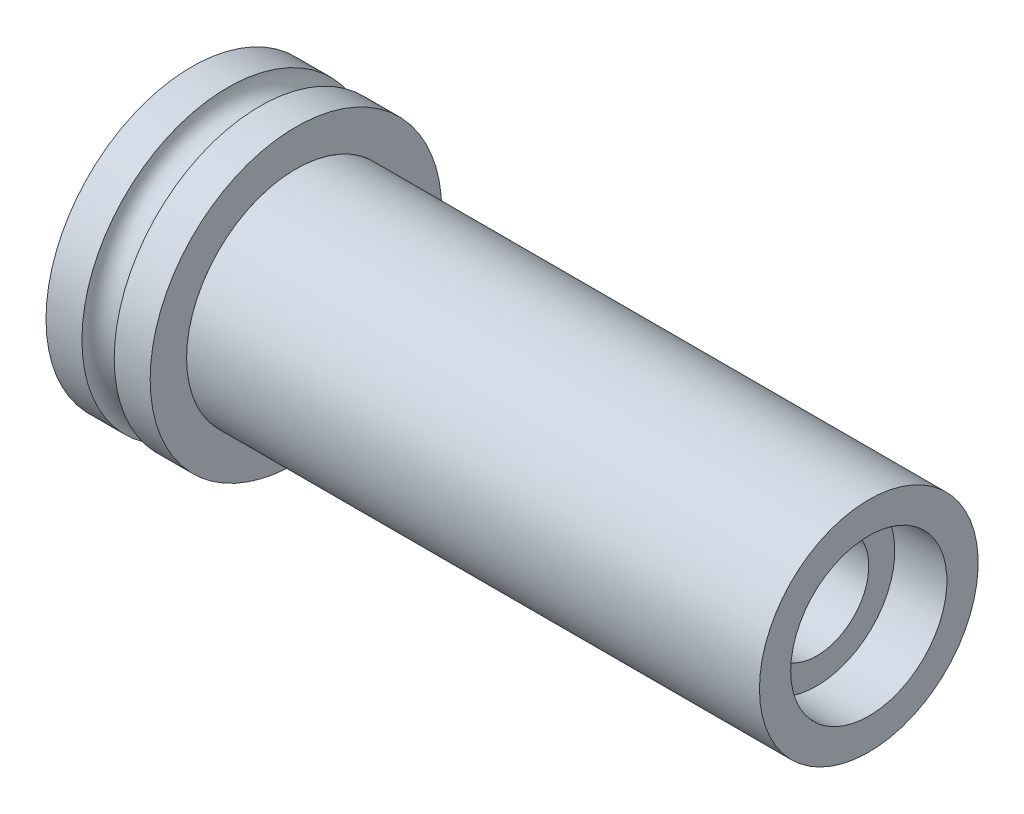
SolidWorks part; units mm, degrees
ref_plane "Front Plane" through (0, 0, 0) normal (0, 0, 1) x (1, 0, 0)
ref_plane "Top Plane" through (0, 0, 0) normal (0, 1, 0) x (1, 0, 0)
ref_plane "Right Plane" through (0, 0, 0) normal (1, 0, 0) x (0, 0, -1)
sketch "Sketch1" plane through (0, 0, 0) normal (0, 1, 0) x (1, 0, 0)
  line L0 (-27.5, 0) -> (27.5, 0) construction
  line L1 (-22.5, 7.5) -> (-22.5, 5)
  line L2 (-27.5, 10.5) -> (27.5, 10.5)
  line L3 (-27.5, 10.5) -> (-27.5, 7.5)
  line L4 (-27.5, 7.5) -> (-22.5, 7.5)
  line L5 (27.5, 10.5) -> (27.5, 7.5)
  line L6 (-27.5, 10.5) -> (27.5, 7.5) construction
  line L7 (-27.5, 7.5) -> (27.5, 10.5) construction
  line L8 (-22.5, 5) -> (22.5, 5)
  line L9 (22.5, 5) -> (22.5, 7.5)
  line L10 (22.5, 7.5) -> (27.5, 7.5)
  point P2 (0, 9)
  point P3 (0, 0)
  dimension "D1" = 55
  dimension "D2" = 3
  dimension "D3" = 7.5
  dimension "D4" = 5
  dimension "D5" = 5
  dimension "D6" = 5
revolve "Revolve1" add sketch "Sketch1" angle 360 about L0
sketch "Sketch2" plane through (-27.5, 0, 0) normal (1, 0, 0) x (0, 0, -1)
  circle A0 centre (0, 0) radius 10.5
  circle A1 centre (0, 0) radius 14
  dimension "D1" = 28
extrude "Boss-Extrude1" add sketch "Sketch2" against normal blind 10
sketch "Sketch3" plane through (0, 0, 0) normal (0, 0, 1) x (1, 0, 0)
  line L0 (-27.5, 14) -> (-37.5, 14) construction
  line L1 (0, 0) -> (29.4523, 0) construction
  circle A0 centre (-32.5, 14) radius 1.55
  dimension "D1" = 3.1
revolve "Cut-Revolve2" cut sketch "Sketch3" angle 360 about L1
